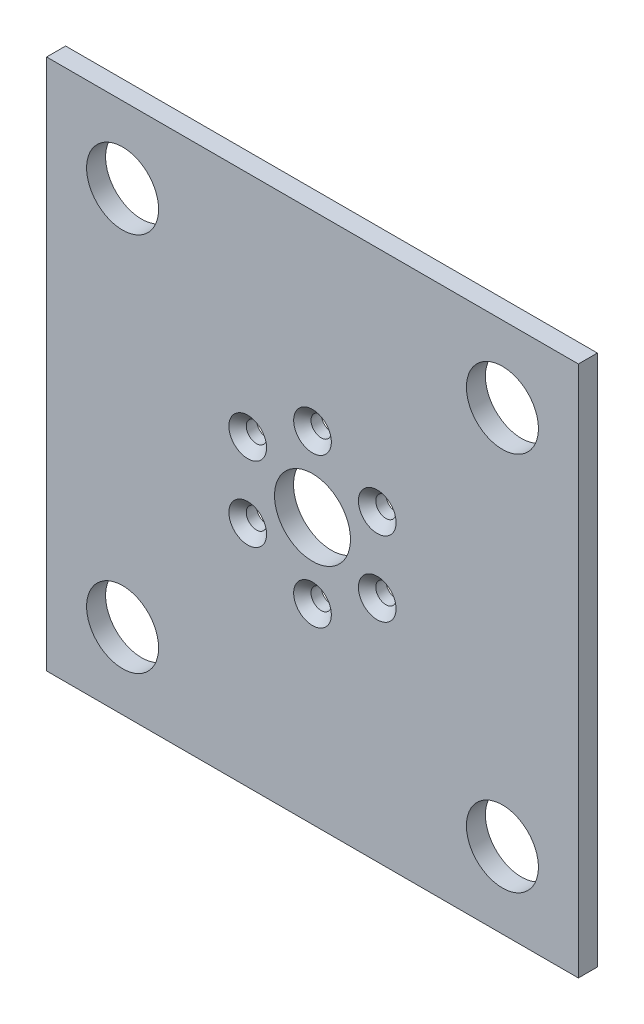
SolidWorks part; units mm, degrees
ref_plane "Front Plane" through (0, 0, 0) normal (0, 0, 1) x (1, 0, 0)
ref_plane "Top Plane" through (0, 0, 0) normal (0, 1, 0) x (1, 0, 0)
ref_plane "Right Plane" through (0, 0, 0) normal (1, 0, 0) x (0, 0, -1)
sketch "Sketch1" plane through (0, 0, 0) normal (0, 0, 1) x (1, 0, 0)
  line L1 (-44.45, -44.45) -> (44.45, -44.45)
  line L2 (-44.45, -44.45) -> (-44.45, 44.45)
  line L3 (-44.45, 44.45) -> (44.45, 44.45)
  line L4 (44.45, -44.45) -> (44.45, 44.45)
  line L5 (-44.45, -44.45) -> (44.45, 44.45) construction
  line L6 (-44.45, 44.45) -> (44.45, -44.45) construction
  point P0 (0, 0)
  dimension "D1" = 88.9
extrude "Boss-Extrude1" add sketch "Sketch1" along normal blind 3.175
sketch "Sketch3" plane through (0, 0, 3.175) normal (0, 0, 1) x (1, 0, 0)
  line L0 (44.45, 44.45) -> (-44.45, 44.45) construction
  line L1 (-44.45, 44.45) -> (-44.45, -44.45) construction
  circle A0 centre (-31.75, 31.75) radius 6.0189
  dimension "D1" = 12.7
  dimension "D2" = 12.7
extrude "Cut-Extrude1" cut sketch "Sketch3" against normal through all
mirror "Mirror1" about plane through (0, 0, 0) normal (1, 0, 0) of "Cut-Extrude1"
mirror "Mirror2" about plane through (0, 0, 0) normal (0, 1, 0) of "Mirror1", "Cut-Extrude1"
sketch "Sketch4" plane through (0, 0, 3.175) normal (0, 0, 1) x (1, 0, 0)
  circle A0 centre (0, 0) radius 6.35
  dimension "D1" = 12.7
extrude "Cut-Extrude2" cut sketch "Sketch4" against normal through all
sketch "Sketch6" plane through (0, 0, 3.175) normal (0, 0, 1) x (1, 0, 0)
  line L0 (0, 0) -> (0, 12.5) construction
  dimension "D1" = 12.5
hole_wizard "CSK for M3 Flat Head Machine Screw1" positions "Sketch9" profile "Sketch10" countersink size "M3" standard "Ansi Metric" end condition through all
sketch "Sketch9" plane through (0, 0, 3.175) normal (0, 0, 1) x (1, 0, 0)
  point P1 (0, 12.5)
sketch "Sketch10" plane through (0, 12.5, 3.175) normal (1, 0, 0) x (0, -1, 0)
  line L0 (0, 0) -> (0, 3.175)
  line L1 (0, 3.175) -> (1.7, 3.175)
  line L2 (1.7, 3.175) -> (1.7, 1.45)
  line L3 (1.7, 1.45) -> (3.15, 0)
  line L5 (3.15, 0) -> (0, 0)
  line L6 (-1.7, 1.45) -> (-3.15, 0) construction
  line L11 (0, -6.35) -> (0, 107.95) construction
  dimension "Thru Hole Dia." = 3.4
  dimension "Thru Hole Depth" = 3.175
  dimension "Near C'Sink Dia." = 6.3
  dimension "Near C'Sink Angle" = 90
pattern_circular "CirPattern1" count 6 over 360 about axis through (0, 0, 0) along (0, 0, 1) of "CSK for M3 Flat Head Machine Screw1"
sketch "Sketch11" plane through (-44.45, 0, 0) normal (-1, 0, 0) x (0, 0, 1)
  line L0 (3.175, 44.45) -> (28.575, 44.45) construction
  line L1 (3.175, 44.45) -> (3.175, -44.45) construction
  dimension "D1" = 25.4
